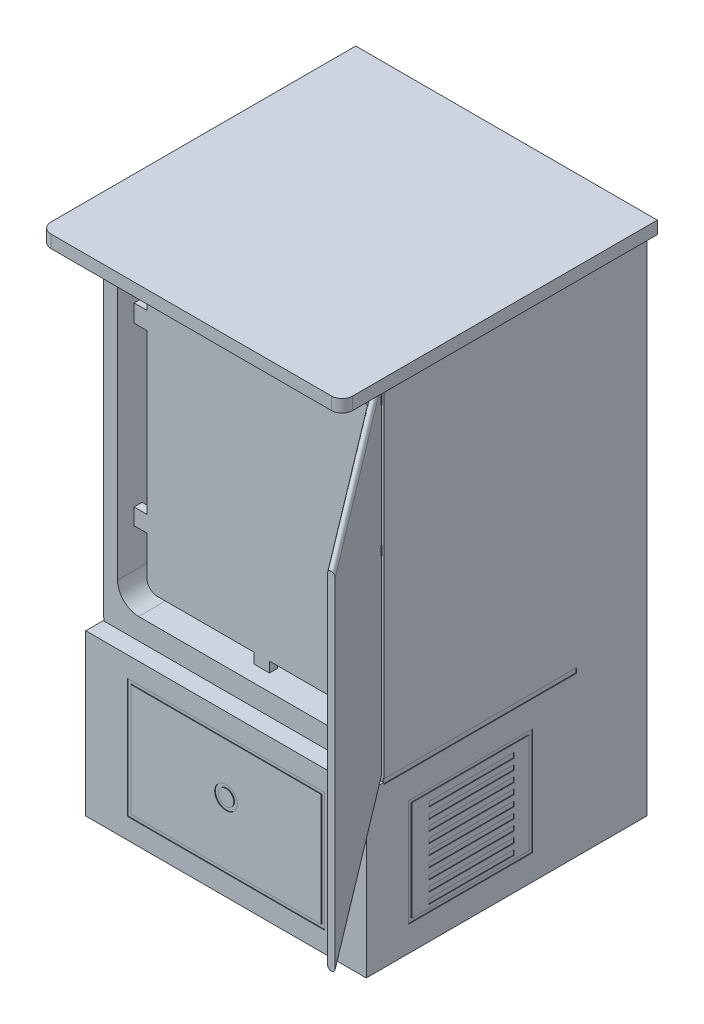
SolidWorks part; units mm, degrees
ref_plane "Alzado" through (0, 0, 0) normal (0, 0, 1) x (1, 0, 0)
ref_plane "Planta" through (0, 0, 0) normal (0, 1, 0) x (1, 0, 0)
ref_plane "Vista lateral" through (0, 0, 0) normal (1, 0, 0) x (0, 0, -1)
sketch "Croquis1" plane through (0, 0, 0) normal (0, 1, 0) x (1, 0, 0)
  line L1 (-400, 300) -> (400, 300)
  line L2 (-400, 300) -> (-400, -300)
  line L3 (-400, -300) -> (400, -300)
  line L4 (400, 300) -> (400, -300)
  line L5 (-400, 300) -> (400, -300) construction
  line L6 (-400, -300) -> (400, 300) construction
  point P0 (0, 0)
  dimension "D1" = 800
  dimension "D2" = 600
extrude "Saliente-Extruir1" add sketch "Croquis1" along normal blind 1000
sketch "Croquis2" plane through (0, 0, 300) normal (0, 0, 1) x (1, 0, 0)
  line L1 (-299.2597, 934.4838) -> (294.2721, 934.4838)
  line L2 (-359.2597, 874.4838) -> (-359.2597, 91.4597)
  line L3 (-299.2597, 31.4597) -> (294.2721, 31.4597)
  line L4 (354.2721, 874.4838) -> (354.2721, 91.4597)
  line L5 (-359.2597, 934.4838) -> (354.2721, 31.4597) construction
  line L6 (-359.2597, 31.4597) -> (354.2721, 934.4838) construction
  arc A0 (-359.2597, 91.4597) -> (-299.2597, 31.4597) centre (-299.2597, 91.4597) ccw
  arc A1 (294.2721, 31.4597) -> (354.2721, 91.4597) centre (294.2721, 91.4597) ccw
  arc A2 (294.2721, 934.4838) -> (354.2721, 874.4838) centre (294.2721, 874.4838) cw
  arc A3 (-299.2597, 934.4838) -> (-359.2597, 874.4838) centre (-299.2597, 874.4838) ccw
  point P0 (-2.4938, 482.9718)
  dimension "D1" = 60
extrude "Cortar-Extruir1" cut sketch "Croquis2" against normal blind 567
sketch "Croquis3" plane through (0, 0, 300) normal (0, 0, 1) x (1, 0, 0)
  line L0 (400, 1000) -> (400, 0) construction
  line L1 (-400, 1000) -> (400, 1000)
  line L2 (-400, 1000) -> (-400, 964.0422)
  line L3 (-400, 964.0422) -> (400, 964.0422)
  line L4 (400, 1000) -> (400, 964.0422)
extrude "Saliente-Extruir2" add sketch "Croquis3" along normal blind 99
sketch "Croquis4" plane through (400, 0, 0) normal (1, 0, 0) x (0, 0, -1)
  line L0 (300, 1000) -> (300, 0) construction
  line L1 (-399, 1000) -> (300, 1000)
  line L2 (-399, 1000) -> (-399, 964.0422)
  line L3 (-399, 964.0422) -> (300, 964.0422)
  line L4 (300, 1000) -> (300, 964.0422)
  line L5 (-399, 964.0422) -> (-399, 1000) construction
extrude "Saliente-Extruir3" add sketch "Croquis4" along normal blind 30
sketch "Croquis5" plane through (-400, 0, 0) normal (-1, 0, 0) x (0, 0, 1)
  line L0 (-300, 1000) -> (-300, 0) construction
  line L1 (399, 1000) -> (-300, 1000)
  line L2 (399, 1000) -> (399, 964.0422)
  line L3 (399, 964.0422) -> (-300, 964.0422)
  line L4 (-300, 1000) -> (-300, 964.0422)
extrude "Saliente-Extruir4" add sketch "Croquis5" along normal blind 30
fillet "Redondeo1" radius 30 2 edges at (430, 982.0211, 399) (-430, 982.0211, 399)
sketch "Croquis6" plane through (0, 0, -300) normal (0, 0, -1) x (-1, 0, 0)
  line L0 (400, 0) -> (-400, 0) construction
  line L1 (400, 0) -> (-400, 0)
  line L2 (400, 0) -> (400, -486.806)
  line L3 (400, -486.806) -> (-400, -486.806)
  line L4 (-400, 0) -> (-400, -486.806)
extrude "Saliente-Extruir5" add sketch "Croquis6" against normal up to surface (600 mm away) up to face at (-2.4938, 482.9718, 300)
sketch "Croquis8" plane through (0, 0, 300) normal (0, 0, 1) x (1, 0, 0)
  line L0 (400, 964.0422) -> (400, -486.806) construction
  line L1 (-400, 964.0422) -> (400, 964.0422)
  line L2 (-400, 964.0422) -> (-400, -29.1398)
  line L3 (-400, -29.1398) -> (400, -29.1398)
  line L4 (400, 964.0422) -> (400, -29.1398)
extrude "Cortar-Extruir3" cut sketch "Croquis8" against normal blind 50
sketch "Croquis9" plane through (-400, 0, 0) normal (-1, 0, 0) x (0, 0, 1)
  line L0 (250, 964.0422) -> (250, -29.1398) construction
  line L1 (-300, -33.9842) -> (250, -33.9842)
  line L2 (-300, -33.9842) -> (-300, -20.3179)
  line L3 (-300, -20.3179) -> (250, -20.3179)
  line L4 (250, -33.9842) -> (250, -20.3179)
  line L5 (-300, -33.9842) -> (250, -20.3179) construction
  line L6 (-300, -20.3179) -> (250, -33.9842) construction
  line L7 (-300, 964.0422) -> (-300, -486.806) construction
  point P0 (-25, -27.151)
extrude "Cortar-Extruir4" cut sketch "Croquis9" against normal blind 2
sketch "Croquis10" plane through (400, 0, 0) normal (1, 0, 0) x (0, 0, -1)
  line L0 (300, -33.9842) -> (-250, -33.9842) construction
  line L1 (300, -20.3179) -> (-250, -20.3179)
  line L2 (300, -20.3179) -> (300, -33.9842)
  line L3 (300, -33.9842) -> (-250, -33.9842)
  line L4 (-250, -20.3179) -> (-250, -33.9842)
  line L5 (300, -33.9842) -> (-250, -33.9842) construction
extrude "Cortar-Extruir5" cut sketch "Croquis10" against normal blind 2
sketch "Croquis11" plane through (-400, 0, 0) normal (-1, 0, 0) x (0, 0, 1)
  line L0 (-164.4809, -119.0564) -> (169.9361, -119.0564)
  line L1 (-174.4809, -109.0564) -> (179.9361, -109.0564)
  line L2 (-174.4809, -109.0564) -> (-174.4809, -414.4003)
  line L3 (-174.4809, -414.4003) -> (179.9361, -414.4003)
  line L4 (179.9361, -109.0564) -> (179.9361, -414.4003)
  line L5 (169.9361, -119.0564) -> (169.9361, -404.4003)
  line L6 (-164.4809, -404.4003) -> (169.9361, -404.4003)
  line L7 (-164.4809, -119.0564) -> (-164.4809, -404.4003)
  dimension "D1" = 10
extrude "Cortar-Extruir6" cut sketch "Croquis11" against normal blind 2
sketch "Croquis12" plane through (400, 0, 0) normal (1, 0, 0) x (0, 0, -1)
  line L1 (164.4809, -119.0564) -> (-169.9361, -119.0564)
  line L2 (164.4809, -119.0564) -> (164.4809, -404.4003)
  line L3 (164.4809, -404.4003) -> (-169.9361, -404.4003)
  line L4 (-169.9361, -119.0564) -> (-169.9361, -404.4003)
  line L5 (-179.9361, -414.4003) -> (174.4809, -414.4003)
  line L6 (-179.9361, -414.4003) -> (-179.9361, -109.0564)
  line L7 (-179.9361, -109.0564) -> (174.4809, -109.0564)
  line L8 (174.4809, -414.4003) -> (174.4809, -109.0564)
extrude "Cortar-Extruir7" cut sketch "Croquis12" against normal blind 2
sketch "Croquis13" plane through (-400, 0, 0) normal (-1, 0, 0) x (0, 0, 1)
  line L1 (-122.0253, -140.6239) -> (121.2843, -140.6239)
  line L2 (-122.0253, -140.6239) -> (-122.0253, -154.5635)
  line L3 (-122.0253, -154.5635) -> (121.2843, -154.5635)
  line L4 (121.2843, -140.6239) -> (121.2843, -154.5635)
extrude "Cortar-Extruir8" cut sketch "Croquis13" against normal blind 2
pattern_linear "MatrizL1" count 9 spacing 30 along (0, -1, 0) of "Cortar-Extruir8"
mirror "Simetría1" about plane through (0, 0, 0) normal (1, 0, 0) of "MatrizL1", "Cortar-Extruir8"
sketch "Croquis14" plane through (0, 0, 300) normal (0, 0, 1) x (1, 0, 0)
  line L0 (0, -29.1398) -> (0, -486.806) construction
  line L1 (-398, -29.1398) -> (398, -29.1398) construction
  line L2 (-400, -486.806) -> (400, -486.806) construction
  line L3 (0, -486.806) -> (0, -257.9729) construction
  line L4 (0, -257.9729) -> (400, -257.9729) construction
  line L5 (400, -29.1398) -> (400, -486.806) construction
  line L6 (-271.6025, -97.6737) -> (271.6025, -97.6737)
  line L7 (-281.6025, -87.6737) -> (281.6025, -87.6737)
  line L8 (-281.6025, -87.6737) -> (-281.6025, -428.2722)
  line L9 (-281.6025, -428.2722) -> (281.6025, -428.2722)
  line L10 (281.6025, -87.6737) -> (281.6025, -428.2722)
  line L11 (-281.6025, -87.6737) -> (281.6025, -428.2722) construction
  line L12 (-281.6025, -428.2722) -> (281.6025, -87.6737) construction
  line L13 (271.6025, -97.6737) -> (271.6025, -418.2722)
  line L14 (-271.6025, -418.2722) -> (271.6025, -418.2722)
  line L15 (-271.6025, -97.6737) -> (-271.6025, -418.2722)
  dimension "D1" = 10
extrude "Cortar-Extruir9" cut sketch "Croquis14" against normal blind 2
sketch "Croquis15" plane through (0, 0, 300) normal (0, 0, 1) x (1, 0, 0)
  circle A0 centre (0, -241.0783) radius 22.2098
  circle A1 centre (0, -241.0783) radius 32.2098
  dimension "D1" = 10
extrude "Cortar-Extruir10" cut sketch "Croquis15" against normal blind 2
sketch "Croquis17" plane through (0, 0, 250) normal (0, 0, 1) x (1, 0, 0)
  line L0 (381.9464, 950.0927) -> (381.9464, -15.6217) construction
  line L1 (392.8622, 950.0927) -> (392.8622, -15.6217)
  line L2 (371.0307, 950.0927) -> (371.0307, -15.6217)
  arc A0 (392.8622, 950.0927) -> (371.0307, 950.0927) centre (381.9464, 950.0927) ccw
  arc A1 (371.0307, -15.6217) -> (392.8622, -15.6217) centre (381.9464, -15.6217) ccw
  point P2 (381.9464, 467.2355)
sketch3d "Croquis3D1"
  line L0 (381.9464, 467.2355, 250) -> (793.4811, 467.3185, 793.1469)
sweep "Barrer1" add profiles "Croquis17" path "Croquis3D1"
sketch "Croquis18" plane through (0, 0, 250) normal (0, 0, 1) x (1, 0, 0)
  line L1 (360.0112, 930.9528) -> (394.7029, 930.9528)
  line L2 (360.0112, 930.9528) -> (360.0112, 900.4232)
  line L3 (360.0112, 900.4232) -> (394.7029, 900.4232)
  line L4 (394.7029, 930.9528) -> (394.7029, 900.4232)
  line L5 (360.0112, 930.9528) -> (394.7029, 900.4232) construction
  line L6 (360.0112, 900.4232) -> (394.7029, 930.9528) construction
  line L7 (346.0825, 23.5014) -> (390.5511, 23.5014)
  line L8 (346.0825, 23.5014) -> (346.0825, -10.0225)
  line L9 (346.0825, -10.0225) -> (390.5511, -10.0225)
  line L10 (390.5511, 23.5014) -> (390.5511, -10.0225)
  line L11 (346.0825, 23.5014) -> (390.5511, -10.0225) construction
  line L12 (346.0825, -10.0225) -> (390.5511, 23.5014) construction
  line L13 (394.7029, 554.1441) -> (360.0112, 554.1441)
  line L14 (394.7029, 554.1441) -> (394.7029, 527.4488)
  line L15 (394.7029, 527.4488) -> (360.0112, 527.4488)
  line L16 (360.0112, 554.1441) -> (360.0112, 527.4488)
  line L17 (394.7029, 554.1441) -> (360.0112, 527.4488) construction
  line L18 (394.7029, 527.4488) -> (360.0112, 554.1441) construction
  point P0 (377.357, 915.688)
  point P6 (368.3168, 6.7394)
  point P12 (377.357, 540.7964)
extrude "Saliente-Extruir6" add sketch "Croquis18" along normal blind 22
fillet "Redondeo2" radius 19 3 edges at (346.0825, 6.7394, 272) (360.0112, 540.7964, 272) (360.0112, 915.688, 272)
sketch "Croquis19" plane through (115.3743, 0, -87.4174) normal (-0.797, 0, 0.6039) x (0.6039, 0, 0.797)
  line L0 (495.2465, 46.9258) -> (495.2465, 884.1633)
  line L1 (515.2465, 6.9258) -> (1050.984, 6.9258)
  line L2 (485.2465, 36.9258) -> (485.2465, 894.1633)
  line L3 (515.2465, 924.1633) -> (1050.984, 924.1633)
  line L4 (1080.984, 36.9258) -> (1080.984, 894.1633)
  line L5 (485.2465, 6.9258) -> (1080.984, 924.1633) construction
  line L6 (485.2465, 924.1633) -> (1080.984, 6.9258) construction
  line L7 (525.2465, 914.1633) -> (1040.984, 914.1633)
  line L8 (1070.984, 46.9258) -> (1070.984, 884.1633)
  line L9 (525.2465, 16.9258) -> (1040.984, 16.9258)
  line L10 (485.2465, 6.9258) -> (1080.984, 6.9258) construction
  line L11 (1080.984, 6.9258) -> (1080.984, 924.1633) construction
  line L12 (1070.984, 16.9258) -> (1070.984, 914.1633) construction
  line L13 (495.2465, 16.9258) -> (1070.984, 16.9258) construction
  line L14 (495.2465, 16.9258) -> (495.2465, 914.1633) construction
  line L15 (485.2465, 6.9258) -> (485.2465, 924.1633) construction
  line L16 (485.2465, 924.1633) -> (1080.984, 924.1633) construction
  line L17 (495.2465, 914.1633) -> (1070.984, 914.1633) construction
  arc A0 (1050.984, 6.9258) -> (1080.984, 36.9258) centre (1050.984, 36.9258) ccw
  arc A1 (1070.984, 46.9258) -> (1040.984, 16.9258) centre (1040.984, 46.9258) cw
  arc A2 (495.2465, 46.9258) -> (525.2465, 16.9258) centre (525.2465, 46.9258) ccw
  arc A3 (515.2465, 6.9258) -> (485.2465, 36.9258) centre (515.2465, 36.9258) cw
  arc A4 (485.2465, 894.1633) -> (515.2465, 924.1633) centre (515.2465, 894.1633) cw
  arc A5 (495.2465, 884.1633) -> (525.2465, 914.1633) centre (525.2465, 884.1633) cw
  arc A6 (1050.984, 924.1633) -> (1080.984, 894.1633) centre (1050.984, 894.1633) cw
  arc A7 (1040.984, 914.1633) -> (1070.984, 884.1633) centre (1040.984, 884.1633) cw
  point P0 (783.1153, 465.5446)
  dimension "D2" = 30
  dimension "D1" = 10
extrude "Cortar-Extruir11" cut sketch "Croquis19" against normal blind 3
ref_plane "Plano1" through (0, 0, 180) normal (0, 0, 1) x (1, 0, 0)
sketch "Croquis20" plane through (0, 0, 180) normal (0, 0, 1) x (1, 0, 0)
  line L0 (354.2721, 874.4838) -> (354.2721, 91.4597) construction
  line L1 (-292.739, 60.8578) -> (301.9909, 60.8578)
  line L2 (-322.739, 90.8578) -> (-322.739, 866.5008)
  line L3 (-292.739, 896.5008) -> (301.9909, 896.5008)
  line L4 (331.9909, 90.8578) -> (331.9909, 866.5008)
  line L5 (-322.739, 60.8578) -> (331.9909, 896.5008) construction
  line L6 (-322.739, 896.5008) -> (331.9909, 60.8578) construction
  line L7 (309.7096, 751.0775) -> (354.2721, 751.0775)
  line L8 (309.7096, 751.0775) -> (309.7096, 704.3831)
  line L9 (309.7096, 704.3831) -> (354.2721, 704.3831)
  line L10 (354.2721, 751.0775) -> (354.2721, 704.3831)
  line L11 (309.7096, 751.0775) -> (354.2721, 704.3831) construction
  line L12 (309.7096, 704.3831) -> (354.2721, 751.0775) construction
  line L13 (-359.2597, 874.4838) -> (-359.2597, 91.4597) construction
  line L14 (309.7096, 223.0139) -> (354.2721, 223.0139)
  line L15 (309.7096, 223.0139) -> (309.7096, 187.0296)
  line L16 (309.7096, 187.0296) -> (354.2721, 187.0296)
  line L17 (354.2721, 223.0139) -> (354.2721, 187.0296)
  line L18 (309.7096, 223.0139) -> (354.2721, 187.0296) construction
  line L19 (309.7096, 187.0296) -> (354.2721, 223.0139) construction
  line L20 (-286.2183, 752.3134) -> (-359.2597, 752.3134)
  line L21 (-286.2183, 752.3134) -> (-286.2183, 702.6565)
  line L22 (-286.2183, 702.6565) -> (-359.2597, 702.6565)
  line L23 (-359.2597, 752.3134) -> (-359.2597, 702.6565)
  line L24 (-286.2183, 752.3134) -> (-359.2597, 702.6565) construction
  line L25 (-286.2183, 702.6565) -> (-359.2597, 752.3134) construction
  line L26 (-359.2597, 91.4597) -> (-359.2597, 874.4838) construction
  line L27 (-286.2183, 248.4841) -> (-359.2597, 248.4841)
  line L28 (-286.2183, 248.4841) -> (-286.2183, 202.2759)
  line L29 (-286.2183, 202.2759) -> (-359.2597, 202.2759)
  line L30 (-359.2597, 248.4841) -> (-359.2597, 202.2759)
  line L31 (-286.2183, 248.4841) -> (-359.2597, 202.2759) construction
  line L32 (-286.2183, 202.2759) -> (-359.2597, 248.4841) construction
  line L33 (294.2721, 934.4838) -> (-299.2597, 934.4838) construction
  line L34 (-24.1279, 858.5178) -> (33.3797, 858.5178)
  line L35 (-24.1279, 858.5178) -> (-24.1279, 934.4838)
  line L36 (-24.1279, 934.4838) -> (33.3797, 934.4838)
  line L37 (33.3797, 858.5178) -> (33.3797, 934.4838)
  line L38 (-24.1279, 858.5178) -> (33.3797, 934.4838) construction
  line L39 (-24.1279, 934.4838) -> (33.3797, 858.5178) construction
  line L40 (294.2721, 31.4597) -> (-299.2597, 31.4597) construction
  line L41 (-17.6173, 90.2559) -> (26.8692, 90.2559)
  line L42 (-17.6173, 90.2559) -> (-17.6173, 31.4597)
  line L43 (-17.6173, 31.4597) -> (26.8692, 31.4597)
  line L44 (26.8692, 90.2559) -> (26.8692, 31.4597)
  line L45 (-17.6173, 90.2559) -> (26.8692, 31.4597) construction
  line L46 (-17.6173, 31.4597) -> (26.8692, 90.2559) construction
  arc A0 (301.9909, 60.8578) -> (331.9909, 90.8578) centre (301.9909, 90.8578) ccw
  arc A1 (301.9909, 896.5008) -> (331.9909, 866.5008) centre (301.9909, 866.5008) cw
  arc A2 (-322.739, 866.5008) -> (-292.739, 896.5008) centre (-292.739, 866.5008) cw
  arc A3 (-292.739, 60.8578) -> (-322.739, 90.8578) centre (-292.739, 90.8578) cw
  point P0 (4.6259, 478.6793)
  point P18 (331.9909, 727.7303)
  point P24 (331.9909, 205.0218)
  point P29 (-322.739, 727.485)
  point P36 (-322.739, 225.38)
  point P44 (4.6259, 896.5008)
  point P50 (4.6259, 60.8578)
  dimension "D1" = 30
extrude "Saliente-Extruir7" add sketch "Croquis20" along normal blind 23 contours A3 L1 A0 L4 L16 L15 L14 L9 L8 L7 A1 L3 A2 L2 | L8 L9 L4 L7 | L10 L7 L4 L9 | L15 L16 L4 L14 | L17 L14 L4 L16 | L34 L37 L3 L35 | L3 L37 L36 L35 | L20 L23 L22 L2 | L22 L21 L20 L2 | L29 L28 L27 L2 | L27 L30 L29 L2 | L44 L41 L42 L1 | L44 L1 L42 L43
sketch "Croquis21" plane through (0, 0, -267) normal (0, 0, 1) x (1, 0, 0)
  line L1 (-267.7019, 362.983) -> (267.7019, 362.983)
  line L2 (-267.7019, 362.983) -> (-267.7019, 345.1478)
  line L3 (-267.7019, 345.1478) -> (267.7019, 345.1478)
  line L4 (267.7019, 362.983) -> (267.7019, 345.1478)
  line L5 (-267.7019, 362.983) -> (267.7019, 345.1478) construction
  line L6 (-267.7019, 345.1478) -> (267.7019, 362.983) construction
  point P0 (0, 354.0654)
extrude "Saliente-Extruir8" add sketch "Croquis21" along normal blind 218
sketch "Croquis22" plane through (0, 0, -300) normal (0, 0, -1) x (-1, 0, 0)
  line L0 (-430, 964.0422) -> (-430, 1000)
  line L1 (-430, 1000) -> (430, 1000)
  line L2 (430, 1000) -> (430, 964.0422)
  line L3 (430, 964.0422) -> (400, 964.0422)
  line L4 (400, 964.0422) -> (400, -486.806)
  line L5 (400, -486.806) -> (-400, -486.806)
  line L6 (-400, -486.806) -> (-400, 964.0422)
  line L7 (-400, 964.0422) -> (-430, 964.0422)
extrude "Saliente-Extruir9" add sketch "Croquis22" along normal blind 200
